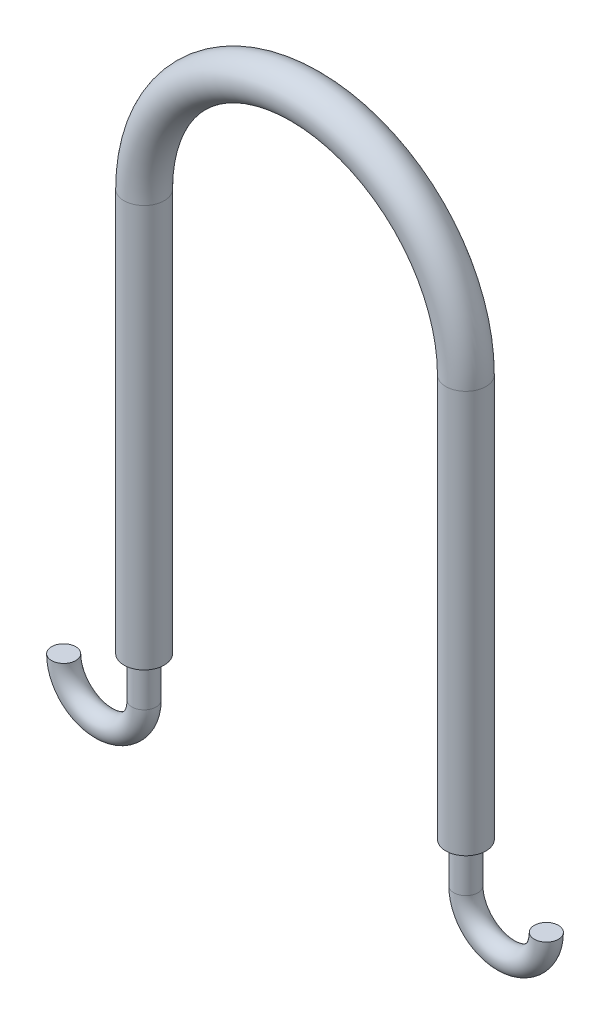
SolidWorks part; units mm, degrees
ref_plane "Front Plane" through (0, 0, 0) normal (0, 0, 1) x (1, 0, 0)
ref_plane "Top Plane" through (0, 0, 0) normal (0, 1, 0) x (1, 0, 0)
ref_plane "Right Plane" through (0, 0, 0) normal (1, 0, 0) x (0, 0, -1)
sketch "Sketch1" plane through (0, 0, 0) normal (0, 0, 1) x (1, 0, 0)
  line L0 (51.2671, -32.523) -> (51.2671, 94.477)
  line L1 (-50.3329, -32.523) -> (-50.3329, 94.477)
  arc A0 (-50.3329, 94.477) -> (51.2671, 94.477) centre (0.4671, 94.477) cw
  dimension "D1" = 127
  dimension "D2" = 101.6
sweep "Sweep1" add path "Sketch1" circular profile diameter 12.7 parameters "D3"=12.7
sketch "Sketch8" plane through (0, 0, 0) normal (0, 0, 1) x (1, 0, 0)
  line L0 (-50.3329, -32.523) -> (-50.3329, -45.223)
  line L1 (-56.6829, -32.523) -> (-43.9829, -32.523) construction
  arc A0 (-50.3329, -45.223) -> (-75.7329, -45.223) centre (-63.0329, -45.223) cw
  point P6 (0, 0)
  dimension "D1" = 12.7
  dimension "D3" = 12.7
sweep "Sweep2" add path "Sketch8" circular profile diameter 7.62 parameters "D3"=7.62
sketch "Sketch16" plane through (0, 0, 0) normal (0, 0, 1) x (1, 0, 0)
  line L0 (51.2671, -32.523) -> (51.2671, -45.223)
  line L1 (44.9171, -32.523) -> (57.6171, -32.523) construction
  arc A0 (51.2671, -45.223) -> (76.6671, -45.223) centre (63.9671, -45.223) ccw
  point P6 (0, 0)
  point P7 (0, 0)
  point P8 (0, 0)
  dimension "D1" = 12.7
  dimension "D2" = 12.7
sweep "Sweep3" add path "Sketch16" circular profile diameter 7.62 parameters "D3"=7.62
